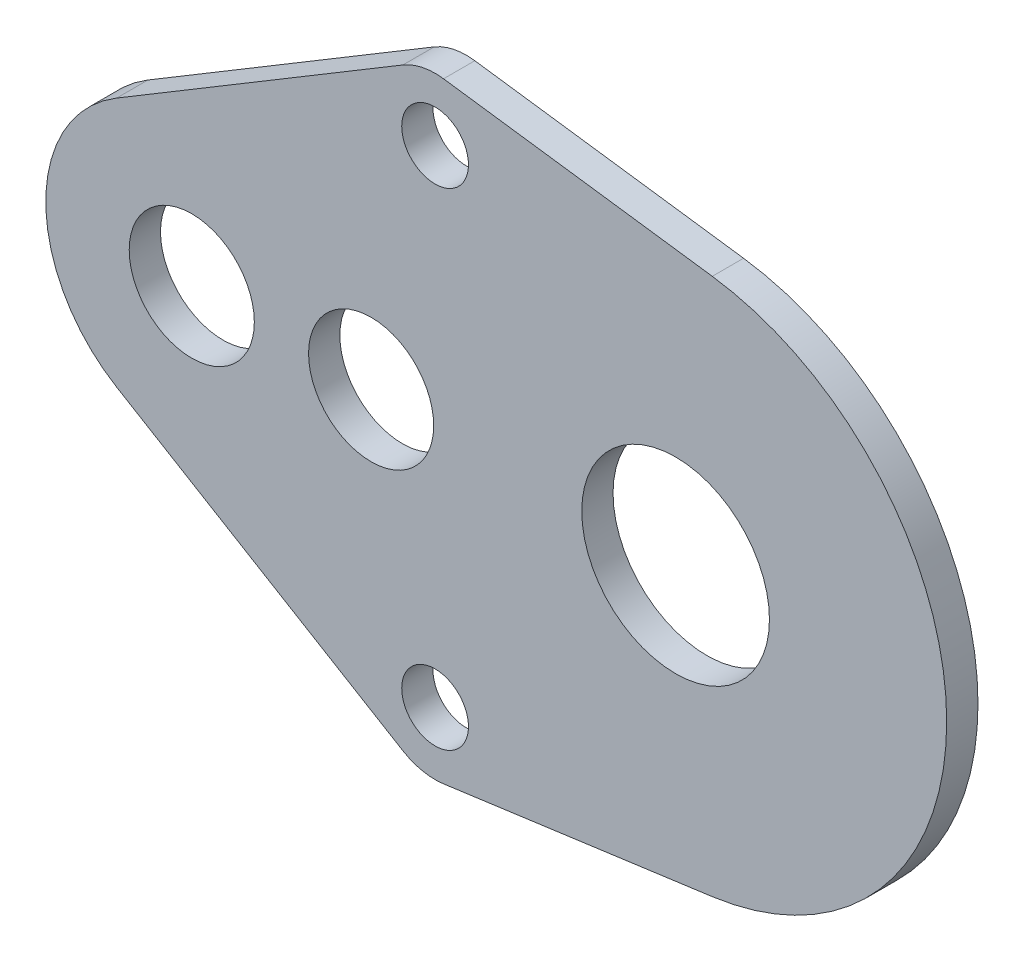
SolidWorks part; units mm, degrees
ref_plane "Front" through (0, 0, 0) normal (0, 0, 1) x (1, 0, 0)
ref_plane "Top" through (0, 0, 0) normal (0, 1, 0) x (1, 0, 0)
ref_plane "Right" through (0, 0, 0) normal (1, 0, 0) x (0, 0, -1)
sketch "Sketch1" plane through (0, 0, 0) normal (0, 0, 1) x (1, 0, 0)
  line L9 (12.0731, 14.6397) -> (24.9585, 12.8805)
  line L15 (12.0731, -14.6397) -> (24.9585, -12.8805)
  line L16 (11.6673, 14.6673) -> (-11.6673, 14.6673)
  line L17 (11.6673, -14.6673) -> (0, -14.6673)
  line L18 (-14.3958, 12.9144) -> (-19.7285, 1.2471)
  line L19 (-18.6976, -2.4735) -> (-1.6976, -14.1408)
  circle A17 centre (0, 0) radius 3
  circle A18 centre (23.2, 0) radius 4.5
  circle A19 centre (8.6, 0) radius 3
  circle A24 centre (-17, 0) radius 1.6
  arc A26 (12.0731, 14.6397) -> (11.6673, 14.6673) centre (11.6673, 11.6673) ccw
  arc A28 (-11.6673, 14.6673) -> (-14.3958, 12.9144) centre (-11.6673, 11.6673) ccw
  arc A29 (11.6673, -14.6673) -> (12.0731, -14.6397) centre (11.6673, -11.6673) ccw
  arc A30 (-1.6976, -14.1408) -> (0, -14.6673) centre (0, -11.6673) ccw
  arc A31 (-19.7285, 1.2471) -> (-18.6976, -2.4735) centre (-17, 0) ccw
  circle A32 centre (0, -11.6673) radius 1.6
  circle A33 centre (11.6673, -11.6673) radius 1.6
  circle A34 centre (-11.6673, 11.6673) radius 1.6
  circle A35 centre (0, 11.6673) radius 1.6
  circle A36 centre (11.6673, 11.6673) radius 1.6
  arc A37 (24.9585, -12.8805) -> (24.9585, 12.8805) centre (23.2, 0) ccw
extrude "Boss-Extrude3" add sketch "Sketch1" along normal blind 1.6
sketch "Sketch2" plane through (0, 0, 1.6) normal (0, 0, 1) x (1, 0, 0)
  line L0 (12.0731, 14.6397) -> (24.9585, 12.8805)
  line L1 (12.0731, -14.6397) -> (24.9585, -12.8805)
  line L2 (9.8187, 14.0301) -> (-3.0809, 3.938)
  line L4 (9.8187, -14.0301) -> (-3.0809, -3.938)
  arc A0 (24.9585, -12.8805) -> (24.9585, 12.8805) centre (23.2, 0) ccw
  arc A1 (-3.0809, 3.938) -> (-3.0809, -3.938) centre (0, 0) ccw
  arc A2 (12.0731, 14.6397) -> (9.8187, 14.0301) centre (11.6673, 11.6673) ccw
  arc A3 (9.8187, -14.0301) -> (12.0731, -14.6397) centre (11.6673, -11.6673) ccw
  circle A4 centre (11.6673, 11.6673) radius 1.6
  circle A5 centre (0, 0) radius 3
  circle A6 centre (8.6, 0) radius 3
  circle A7 centre (23.2, 0) radius 4.5
  circle A8 centre (11.6673, -11.6673) radius 1.6
extrude "Boss-Extrude4" add sketch "Sketch2" along normal blind 1.5
sketch "Sketch3" plane through (0, 0, 0) normal (0, 0, -1) x (-1, 0, 0)
  circle A0 centre (0, 0) radius 63.2066
extrude "Cut-Extrude1" cut sketch "Sketch3" against normal blind 1.6
sketch "Sketch4" plane through (0, 0, 3.1) normal (0, 0, 1) x (1, 0, 0)
  line L0 (-3.6022, 6.002) -> (10.1235, 14.2396)
  line L1 (14.6673, 11.6673) -> (14.6673, -11.6673)
  line L2 (-3.6022, -6.002) -> (10.1235, -14.2396)
  arc A0 (14.6673, 11.6673) -> (10.1235, 14.2396) centre (11.6673, 11.6673) ccw
  arc A1 (10.1235, -14.2396) -> (14.6673, -11.6673) centre (11.6673, -11.6673) ccw
  arc A2 (-3.6022, 6.002) -> (-3.6022, -6.002) centre (0, 0) ccw
  circle A3 centre (0, 0) radius 3
  circle A4 centre (8.6, 0) radius 3
  circle A5 centre (11.6673, 11.6673) radius 1.6
  circle A6 centre (11.6673, -11.6673) radius 1.6
extrude "Boss-Extrude5" add sketch "Sketch4" against normal up to surface (1.5 mm away) up to face at (-3, 0, 1.6)
